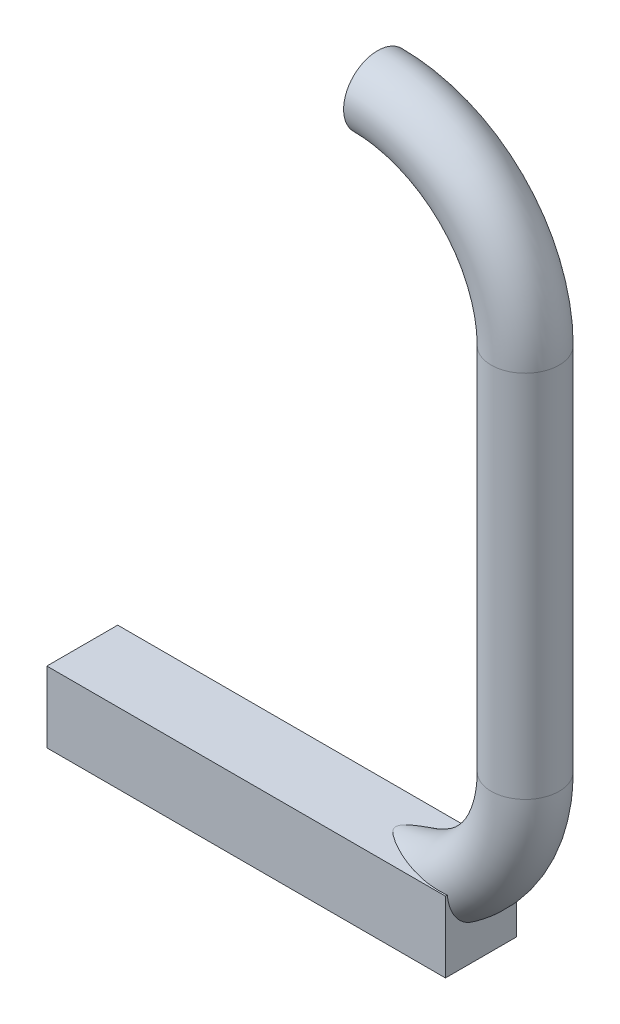
SolidWorks part; units mm, degrees
ref_plane "Plano frontal" through (0, 0, 0) normal (0, 0, 1) x (1, 0, 0)
ref_plane "Plano superior" through (0, 0, 0) normal (0, 1, 0) x (1, 0, 0)
ref_plane "Plano direito" through (0, 0, 0) normal (1, 0, 0) x (0, 0, -1)
sketch "Esboço1" plane through (0, 0, 0) normal (0, 0, 1) x (1, 0, 0)
  line L0 (0, 0) -> (0, 25)
  arc A0 (0, 0) -> (-10, -10) centre (-10, 0) cw
  arc A1 (0, 25) -> (-10, 35) centre (-10, 25) ccw
  dimension "D2" = 10
  dimension "D3" = 10
  dimension "D1" = 25
sweep "Varredura1" add path "Esboço1" circular profile diameter 4.6 parameters "D3"=4.6
sketch "Esboço18" plane through (-10, 0, 0) normal (-1, 0, 0) x (0, 0, 1)
  line L1 (-2.4, -7.6) -> (2.4, -7.6)
  line L2 (-2.4, -7.6) -> (-2.4, -12.4)
  line L3 (-2.4, -12.4) -> (2.4, -12.4)
  line L4 (2.4, -7.6) -> (2.4, -12.4)
  line L5 (-2.4, -7.6) -> (2.4, -12.4) construction
  line L6 (-2.4, -12.4) -> (2.4, -7.6) construction
  circle A0 centre (0, -10) radius 2.3 construction
  point P0 (0, -10)
  dimension "D1" = 4.8
extrude "Ressalto-extrusão1" add sketch "Esboço18" along normal blind 20 and the other way blind 7
